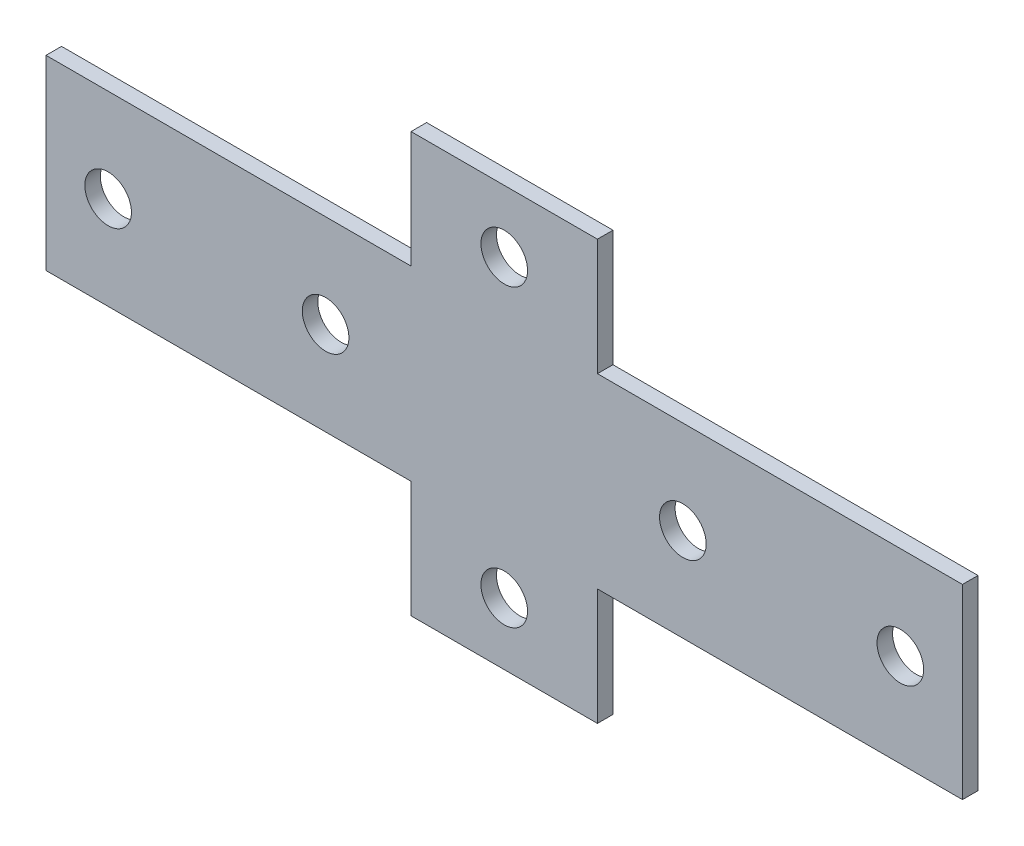
SolidWorks part; units mm, degrees
ref_plane "Спереди" through (0, 0, 0) normal (0, 0, 1) x (1, 0, 0)
ref_plane "Сверху" through (0, 0, 0) normal (0, 1, 0) x (1, 0, 0)
ref_plane "Справа" through (0, 0, 0) normal (1, 0, 0) x (0, 0, -1)
sketch "Эскиз1" plane through (0, 0, 0) normal (0, 0, 1) x (1, 0, 0)
  line L0 (18, -18) -> (88.5, -18)
  line L1 (-88.5, 18) -> (-18, 18)
  line L2 (-88.5, 18) -> (-88.5, -18)
  line L3 (-88.5, -18) -> (-18, -18)
  line L4 (88.5, 18) -> (88.5, -18)
  line L5 (-88.5, 18) -> (88.5, -18) construction
  line L6 (-88.5, -18) -> (88.5, 18) construction
  line L7 (-18, -40.5) -> (18, -40.5)
  line L8 (-18, -40.5) -> (-18, -18)
  line L9 (-18, 40.5) -> (18, 40.5)
  line L10 (18, -40.5) -> (18, -18)
  line L11 (-18, -40.5) -> (18, 40.5) construction
  line L12 (-18, 40.5) -> (18, -40.5) construction
  line L13 (18, 18) -> (88.5, 18)
  line L14 (-18, 18) -> (-18, 40.5)
  line L15 (18, 18) -> (18, 40.5)
  line L16 (0, 28.5) -> (0, -28.5) construction
  line L17 (0, 28.5) -> (0, 40.5) construction
  line L18 (-76.5, 0) -> (-88.5, 0) construction
  circle A0 centre (0, 28.5) radius 4.5
  circle A1 centre (0, -28.5) radius 4.5
  circle A2 centre (-76.5, 0) radius 4.5
  circle A3 centre (-34.5, 0) radius 4.5
  circle A4 centre (34.5, 0) radius 4.5
  circle A5 centre (76.5, 0) radius 4.5
  point P0 (0, 0)
  point P6 (0, 0)
  dimension "D4" = 12
  dimension "D5" = 9
  dimension "D6" = 42
  dimension "D1" = 177
  dimension "D2" = 81
  dimension "D3" = 36
extrude "Бобышка-Вытянуть1" add sketch "Эскиз1" along normal blind 3
